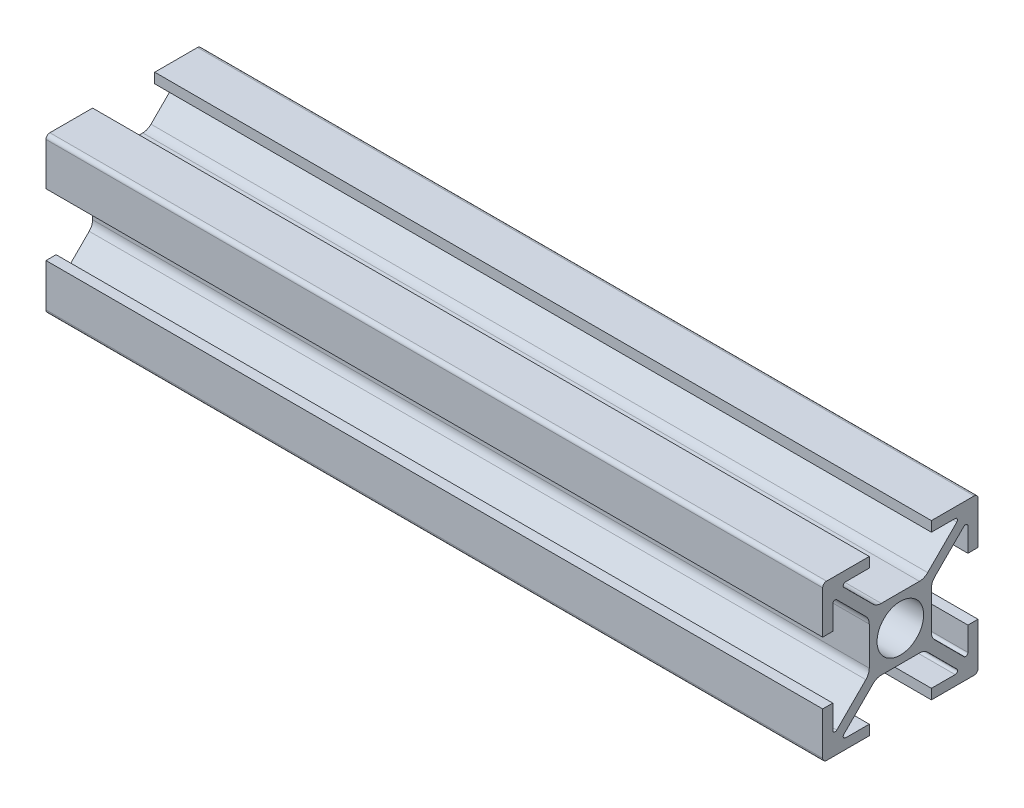
SolidWorks part; units mm, degrees
ref_plane "Plano frontal" through (0, 0, 0) normal (0, 0, 1) x (1, 0, 0)
ref_plane "Plano superior" through (0, 0, 0) normal (0, 1, 0) x (1, 0, 0)
ref_plane "Plano direito" through (0, 0, 0) normal (1, 0, 0) x (0, 0, -1)
sketch "Esboço1" plane through (0, 0, 0) normal (0, 0, 1) x (1, 0, 0)
  line L0 (0, 0) -> (100, 0)
  dimension "D1" = 100
other "Quadrado PF20-01 - PERFIL 2020 BÁSICO(1)"
ref_plane "Plano1" through (0, 0, 0) normal (1, 0, 0) x (0, 1, 0)
sketch "Sketch1" plane through (0, 0, 0) normal (1, 0, 0) x (0, 1, 0)
  line L0 (8.1879, -7.2686) -> (4.4393, -3.5201)
  line L1 (4, -2.4594) -> (4, 2.4594)
  line L2 (4.4393, 3.5201) -> (8.1879, 7.2686)
  line L3 (8.7, 7.0565) -> (8.7, 4)
  line L4 (8.7, 4) -> (10, 4)
  line L5 (10, 4) -> (10, 9.5)
  line L6 (9.5, 10) -> (4, 10)
  line L7 (4, 10) -> (4, 8.7)
  line L8 (4, 8.7) -> (7.0565, 8.7)
  line L9 (7.2686, 8.1879) -> (3.5201, 4.4393)
  line L10 (2.4594, 4) -> (-2.4594, 4)
  line L11 (-3.5201, 4.4393) -> (-7.2686, 8.1879)
  line L12 (-7.0565, 8.7) -> (-4, 8.7)
  line L13 (-4, 8.7) -> (-4, 10)
  line L14 (-4, 10) -> (-9.5, 10)
  line L15 (-10, 9.5) -> (-10, 4)
  line L16 (-10, 4) -> (-8.7, 4)
  line L17 (-8.7, 4) -> (-8.7, 7.0565)
  line L18 (-8.1879, 7.2686) -> (-4.4393, 3.5201)
  line L19 (-4, 2.4594) -> (-4, -2.4594)
  line L20 (-4.4393, -3.5201) -> (-8.1879, -7.2686)
  line L21 (-8.7, -7.0565) -> (-8.7, -4)
  line L22 (-8.7, -4) -> (-10, -4)
  line L23 (-10, -4) -> (-10, -9.5)
  line L24 (-9.5, -10) -> (-4, -10)
  line L25 (-4, -10) -> (-4, -8.7)
  line L26 (-4, -8.7) -> (-7.0565, -8.7)
  line L27 (-7.2686, -8.1879) -> (-3.5201, -4.4393)
  line L28 (-2.4594, -4) -> (2.4594, -4)
  line L29 (3.5201, -4.4393) -> (7.2686, -8.1879)
  line L30 (7.0565, -8.7) -> (4, -8.7)
  line L31 (4, -8.7) -> (4, -10)
  line L32 (4, -10) -> (9.5, -10)
  line L33 (10, -9.5) -> (10, -4)
  line L34 (10, -4) -> (8.7, -4)
  line L35 (8.7, -4) -> (8.7, -7.0565)
  circle A0 centre (0, 0) radius 3
  arc A1 (8.1879, -7.2686) -> (8.7, -7.0565) centre (8.4, -7.0565) ccw
  arc A2 (4, -2.4594) -> (4.4393, -3.5201) centre (5.5, -2.4594) ccw
  arc A3 (4.4393, 3.5201) -> (4, 2.4594) centre (5.5, 2.4594) ccw
  arc A4 (8.7, 7.0565) -> (8.1879, 7.2686) centre (8.4, 7.0565) ccw
  arc A5 (10, 9.5) -> (9.5, 10) centre (9.5, 9.5) ccw
  arc A6 (7.2686, 8.1879) -> (7.0565, 8.7) centre (7.0565, 8.4) ccw
  arc A7 (2.4594, 4) -> (3.5201, 4.4393) centre (2.4594, 5.5) ccw
  arc A8 (-3.5201, 4.4393) -> (-2.4594, 4) centre (-2.4594, 5.5) ccw
  arc A9 (-7.0565, 8.7) -> (-7.2686, 8.1879) centre (-7.0565, 8.4) ccw
  arc A10 (-9.5, 10) -> (-10, 9.5) centre (-9.5, 9.5) ccw
  arc A11 (-8.1879, 7.2686) -> (-8.7, 7.0565) centre (-8.4, 7.0565) ccw
  arc A12 (-4, 2.4594) -> (-4.4393, 3.5201) centre (-5.5, 2.4594) ccw
  arc A13 (-4.4393, -3.5201) -> (-4, -2.4594) centre (-5.5, -2.4594) ccw
  arc A14 (-8.7, -7.0565) -> (-8.1879, -7.2686) centre (-8.4, -7.0565) ccw
  arc A15 (-10, -9.5) -> (-9.5, -10) centre (-9.5, -9.5) ccw
  arc A16 (-7.2686, -8.1879) -> (-7.0565, -8.7) centre (-7.0565, -8.4) ccw
  arc A17 (-2.4594, -4) -> (-3.5201, -4.4393) centre (-2.4594, -5.5) ccw
  arc A18 (3.5201, -4.4393) -> (2.4594, -4) centre (2.4594, -5.5) ccw
  arc A19 (7.0565, -8.7) -> (7.2686, -8.1879) centre (7.0565, -8.4) ccw
  arc A20 (9.5, -10) -> (10, -9.5) centre (9.5, -9.5) ccw
  point P0 (0, 10)
  point P1 (-10, 10)
  point P2 (10, 10)
  point P3 (10, 0)
  point P4 (10, -10)
  point P5 (0, -10)
  point P6 (-10, -10)
  point P7 (-10, 0)
  point P8 (0, 0)
  point P87 (0, 0)
